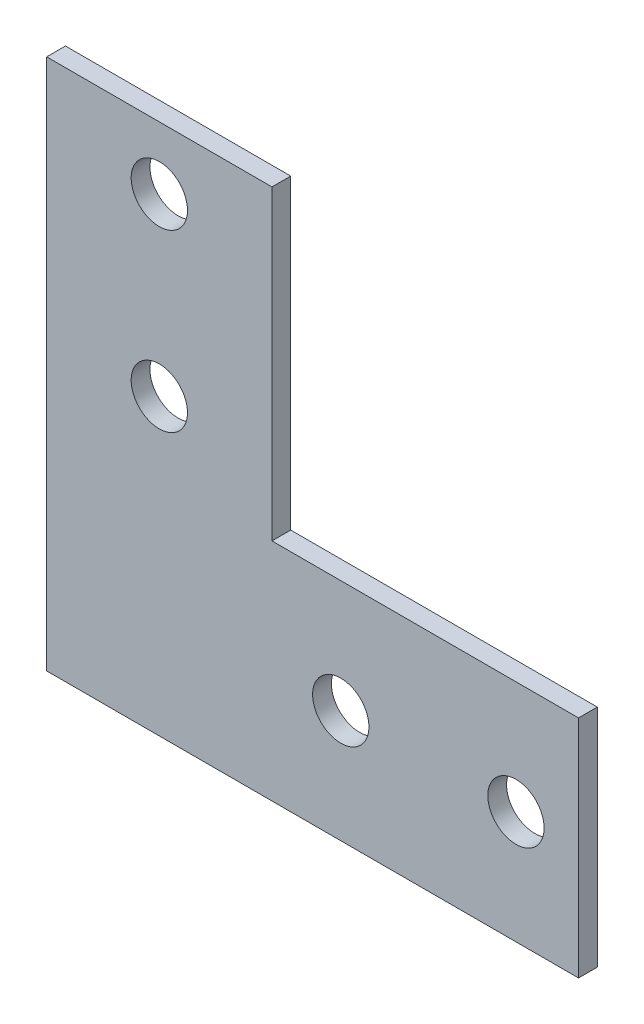
SolidWorks part; units mm, degrees
ref_plane "Спереди" through (0, 0, 0) normal (0, 0, 1) x (1, 0, 0)
ref_plane "Сверху" through (0, 0, 0) normal (0, 1, 0) x (1, 0, 0)
ref_plane "Справа" through (0, 0, 0) normal (1, 0, 0) x (0, 0, -1)
sketch "Эскиз1" plane through (0, 0, 0) normal (0, 0, 1) x (1, 0, 0)
  line L5 (0, 85) -> (0, 0)
  line L6 (0, 0) -> (85, 0)
  line L11 (85, 0) -> (85, 36)
  line L12 (85, 36) -> (36, 36)
  line L16 (36, 36) -> (36, 85)
  line L17 (36, 85) -> (0, 85)
  line L18 (85, 18) -> (75, 18) construction
  line L19 (75, 18) -> (47, 18) construction
  line L20 (18, 85) -> (18, 75) construction
  line L21 (18, 75) -> (18, 47) construction
  circle A6 centre (18, 75) radius 4.5
  circle A7 centre (18, 47) radius 4.5
  circle A8 centre (47, 18) radius 4.5
  circle A9 centre (75, 18) radius 4.5
  dimension "D4" = 10
  dimension "D5" = 28
  dimension "D3" = 9
  dimension "D1" = 85
  dimension "D2" = 36
extrude "Бобышка-Вытянуть1" add sketch "Эскиз1" along normal blind 3
